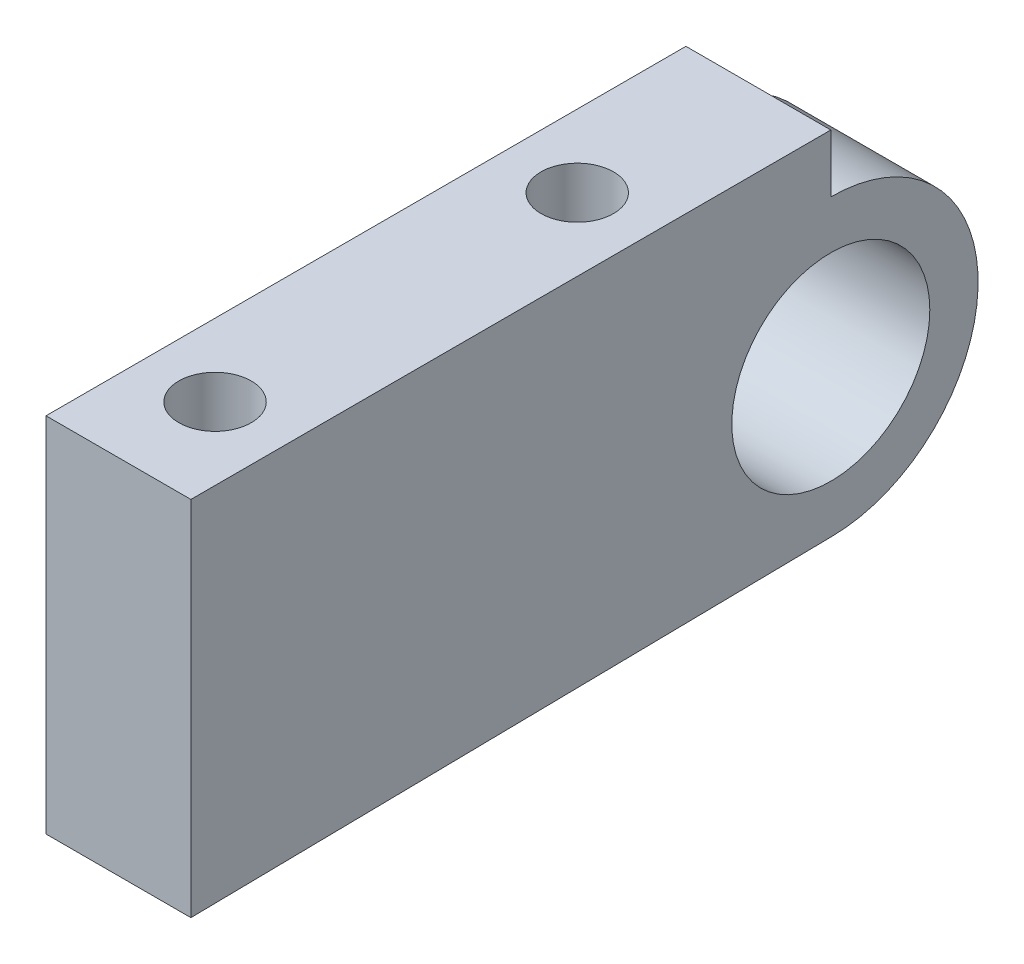
SolidWorks part; units mm, degrees
material "6061-T6 (SS)"
ref_plane "前视基准面" through (0, 0, 0) normal (0, 0, 1) x (1, 0, 0)
ref_plane "上视基准面" through (0, 0, 0) normal (0, 1, 0) x (1, 0, 0)
ref_plane "右视基准面" through (0, 0, 0) normal (1, 0, 0) x (0, 0, -1)
sketch "草图1" plane through (0, 0, 0) normal (1, 0, 0) x (0, 0, -1)
  line L1 (-17.5, 7.5) -> (17.5, 7.5)
  line L2 (-17.5, 7.5) -> (-17.5, -7.5)
  line L3 (-17.5, -7.5) -> (17.5, -7.5)
  line L4 (17.5, 7.5) -> (17.5, -7.5)
  line L5 (0, -7.5) -> (0, 7.5) construction
  line L6 (-17.5, 0) -> (17.5, 0) construction
  point P0 (0, 0)
  dimension "D1" = 15
  dimension "D2" = 35
extrude "凸台-拉伸1" add sketch "草图1" along normal blind 6
sketch "草图2" plane through (0, 7.5, 0) normal (0, 1, 0) x (1, 0, 0)
  line L0 (3, -12.5) -> (3, -50012.5) construction
  line L1 (6, -17.5) -> (0, -17.5) construction
  circle A0 centre (3, -13.5) radius 1.5
  circle A1 centre (3, 1.5) radius 1.5
  point P4 (3, -17.5)
  dimension "D1" = 3
  dimension "D2" = 15
  dimension "D3" = 4
extrude "切除-拉伸1" cut sketch "草图2" against normal through all
cosmetic thread "装饰螺纹线1" parameters "D2"=4
cosmetic thread "装饰螺纹线2" parameters "D2"=4
sketch "草图3" plane through (6, 0, 0) normal (1, 0, 0) x (0, 0, -1)
  line L0 (17.5, 7.5) -> (-17.5, 7.5) construction
  line L1 (17.5, -7.5) -> (17.5, 7.5) construction
  circle A3 centre (9, -1) radius 4.1
  dimension "D1" = 8.2
  dimension "D2" = 8.5
  dimension "D3" = 8.5
extrude "切除-拉伸2" cut sketch "草图3" against normal through all
sketch "草图4" plane through (6, 0, 0) normal (1, 0, 0) x (0, 0, -1)
  line L0 (9, 5.1) -> (9, 7.5)
  line L1 (17.5, 7.5) -> (-17.5, 7.5) construction
  line L2 (9, 7.5) -> (17.5, 7.5)
  line L3 (17.5, 7.5) -> (17.5, -7.5)
  line L4 (17.5, -7.5) -> (-17.5, -7.5)
  line L5 (-17.5, -7.5) -> (9.0919, -7.0993)
  arc A0 (9.0919, -7.0993) -> (9, 5.1) centre (9, -1) ccw
  circle A1 centre (9, -1) radius 4.1 construction
  dimension "D1" = 2
extrude "切除-拉伸3" cut sketch "草图4" against normal through all
